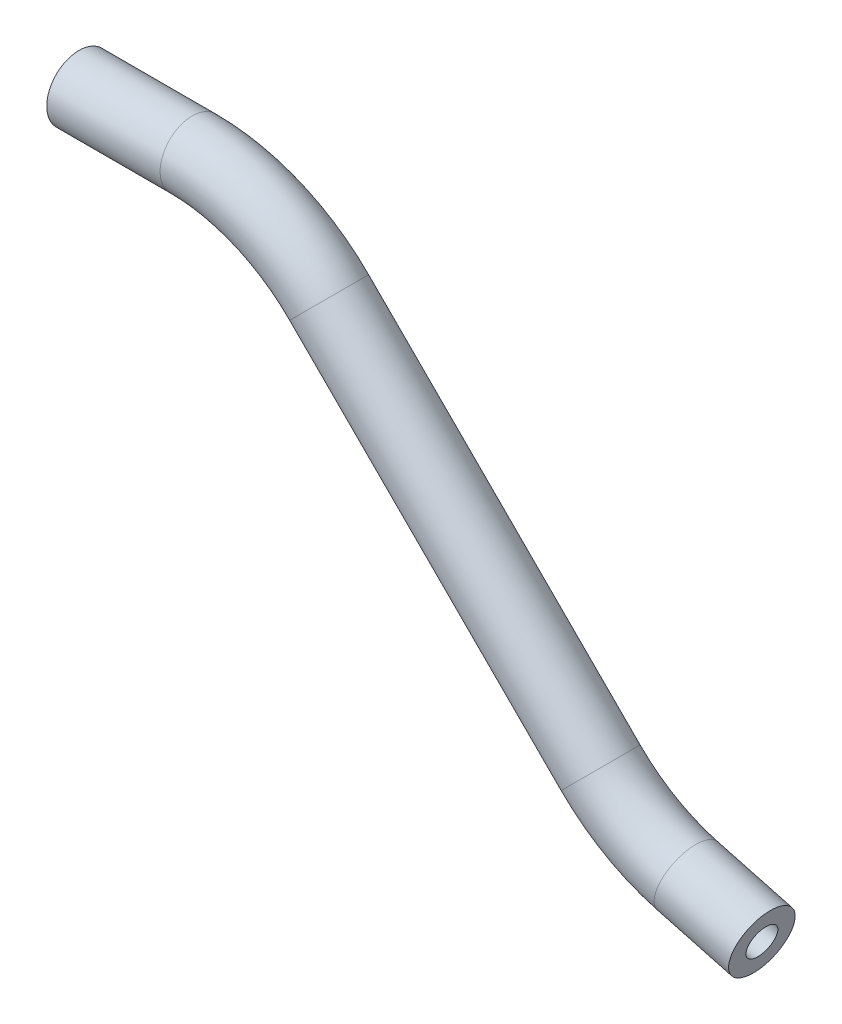
SolidWorks part; units mm, degrees
material "6061-T6 (SS)"
ref_plane "Front Plane" through (0, 0, 0) normal (0, 0, 1) x (1, 0, 0)
ref_plane "Top Plane" through (0, 0, 0) normal (0, 1, 0) x (1, 0, 0)
ref_plane "Right Plane" through (0, 0, 0) normal (1, 0, 0) x (0, 0, -1)
sketch "Sketch1" plane through (0, 0, 0) normal (0, 0, 1) x (1, 0, 0)
  line L0 (0, 0) -> (11.1592, 0)
  line L1 (24.6296, -5.5796) -> (51.3616, -32.3116)
  line L2 (59.9015, -37.2421) -> (67.2383, -39.208)
  line L3 (0, 0) -> (37.3712, 0) construction
  line L4 (51.3616, -32.3116) -> (24.6296, -5.5796) construction
  line L5 (24.6296, -5.5796) -> (3.9972, 15.0528) construction
  line L6 (24.6296, -5.5796) -> (51.3616, -32.3116) construction
  line L7 (51.3616, -32.3116) -> (51.416, -32.366) construction
  line L8 (67.2383, -39.208) -> (59.9015, -37.2421) construction
  line L9 (59.9015, -37.2421) -> (40.7606, -32.1134) construction
  arc A0 (11.1592, 0) -> (24.6296, -5.5796) centre (11.1592, -19.05) cw
  arc A1 (51.3616, -32.3116) -> (59.9015, -37.2421) centre (64.832, -18.8413) ccw
  point P13 (19.05, 0)
  point P14 (54.971, -35.921)
  point P15 (0, 0)
  dimension "D1" = 19.05
  dimension "D2" = 19.05
  dimension "D3" = 45
  dimension "D4" = 30
  dimension "D5" = 19.05
  dimension "D6" = 50.8
  dimension "D7" = 12.7
ref_plane "Plane1" through (0, 0, 0) normal (1, 0, 0) x (0, 0, -1)
sketch "Sketch2" plane through (0, 0, 0) normal (1, 0, 0) x (0, 0, -1)
  circle A0 centre (0, 0) radius 3.175
  circle A1 centre (0, 0) radius 1.524
  dimension "D1" = 6.35
  dimension "D2" = 3.048
sweep "Sweep1" add profiles "Sketch2" path "Sketch1"
